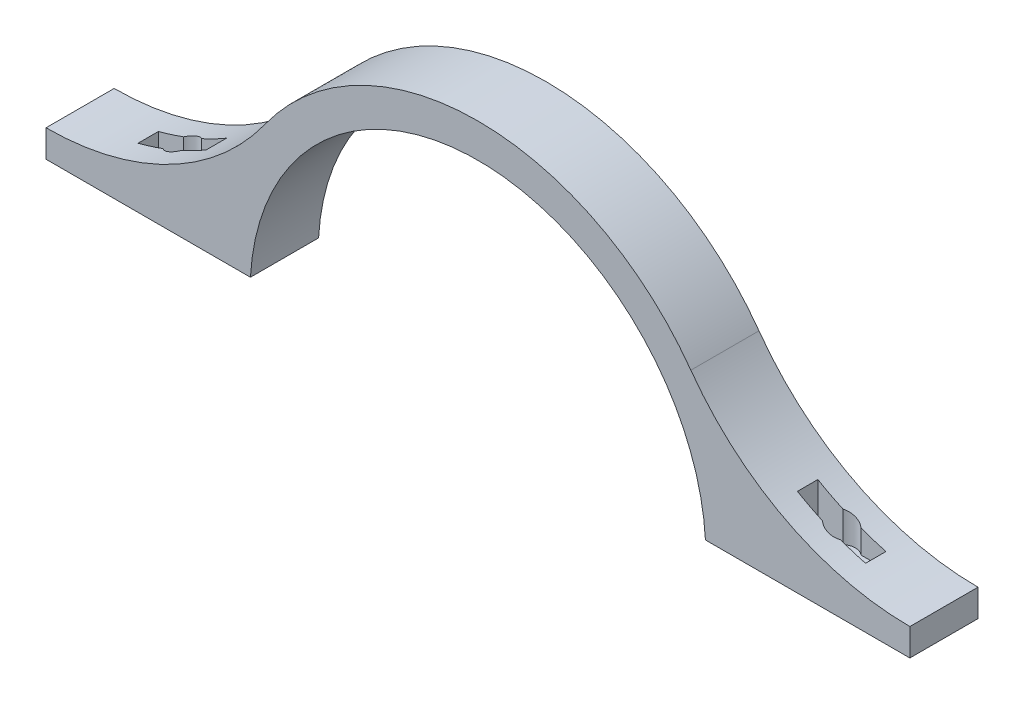
SolidWorks part; units mm, degrees
material "PET"
ref_plane "Front Plane" through (0, 0, 0) normal (0, 0, 1) x (1, 0, 0)
ref_plane "Top Plane" through (0, 0, 0) normal (0, 1, 0) x (1, 0, 0)
ref_plane "Right Plane" through (0, 0, 0) normal (1, 0, 0) x (0, 0, -1)
sketch "Sketch1" plane through (0, 0, 0) normal (0, 0, 1) x (1, 0, 0)
  line L1 (-160.9976, 4.7625) -> (-160.9976, 14.9225)
  line L3 (0, 97.6312) -> (0, 84.9312)
  line L5 (0, 4.7625) -> (-84.7976, 4.7625) construction
  line L6 (0, 0) -> (0, 4.7625)
  line L8 (-84.7976, 4.7625) -> (-160.9976, 4.7625)
  arc A0 (0, 97.6312) -> (-79.3657, 56.859) centre (0, 0) ccw
  circle A5 centre (0, 0) radius 97.6313 construction
  circle A6 centre (0, 0) radius 84.9312 construction
  arc A7 (0, 84.9312) -> (-84.7976, 4.7625) centre (0, 0) ccw
  circle A8 centre (0, 0) radius 84.9312 construction
  arc A10 (-160.9976, 14.9225) -> (-79.3657, 56.859) centre (-160.9976, 115.3415) ccw
  dimension "D3" = 10.16
  dimension "D1" = 12.7
  dimension "D2" = 76.2
  dimension "D5" = 4.7625
extrude "Boss-Extrude1" add sketch "Sketch1" against normal blind 25.4 contours A10 L1 L8 A7 L3 A0
sketch "Sketch3" plane through (0, 4.7625, 0) normal (0, -1, 0) x (1, 0, 0)
  line L0 (-122.8976, 0) -> (-122.8976, -12.7) construction
  line L1 (-84.7976, 0) -> (-160.9976, 0) construction
  line L2 (-122.8976, -12.7) -> (-160.9976, -12.7) construction
  line L3 (-160.9976, -25.4) -> (-160.9976, 0) construction
  line L4 (-119.5375, -16.51) -> (-110.1976, -16.51)
  line L5 (-135.5976, -8.89) -> (-126.2577, -8.89)
  line L6 (-135.5976, -8.89) -> (-135.5976, -16.51)
  line L7 (-135.5976, -16.51) -> (-126.2577, -16.51)
  line L8 (-110.1976, -8.89) -> (-110.1976, -16.51)
  line L9 (-135.5976, -8.89) -> (-110.1976, -16.51) construction
  line L10 (-135.5976, -16.51) -> (-110.1976, -8.89) construction
  line L11 (-119.5375, -8.89) -> (-110.1976, -8.89)
  arc A0 (-126.2577, -16.51) -> (-119.5375, -16.51) centre (-122.8976, -12.7) ccw
  arc A1 (-119.5375, -8.89) -> (-126.2577, -8.89) centre (-122.8976, -12.7) ccw
  dimension "D1" = 10.16
  dimension "D2" = 25.4
  dimension "D3" = 7.62
extrude "Cut-Extrude2" cut sketch "Sketch3" against normal up to surface (23.9572 mm away)
mirror "Mirror2" about plane through (0, 0, -25.4) normal (-1, 0, 0) of "Boss-Extrude1", "Cut-Extrude2"
sketch "Sketch4" plane through (0, 4.7625, 0) normal (0, -1, 0) x (1, 0, 0)
  line L0 (-110.1976, -8.89) -> (-119.5375, -8.89) construction
  line L1 (-110.1976, -16.51) -> (-110.1976, -8.89) construction
  line L2 (-119.5375, -16.51) -> (-110.1976, -16.51) construction
  line L3 (-135.5976, -16.51) -> (-126.2577, -16.51) construction
  line L4 (-135.5976, -8.89) -> (-135.5976, -16.51) construction
  line L5 (-126.2577, -8.89) -> (-135.5976, -8.89) construction
  line L6 (-110.1976, -8.89) -> (-119.5375, -8.89)
  line L7 (-110.1976, -16.51) -> (-110.1976, -8.89)
  line L8 (-119.5375, -16.51) -> (-110.1976, -16.51)
  line L9 (-135.5976, -16.51) -> (-126.2577, -16.51)
  line L10 (-135.5976, -8.89) -> (-135.5976, -16.51)
  line L11 (-126.2577, -8.89) -> (-135.5976, -8.89)
  arc A0 (-119.5375, -8.89) -> (-126.2577, -8.89) centre (-122.8976, -12.7) ccw
  circle A6 centre (-122.8976, -12.7) radius 2.159
  circle A7 centre (-122.8976, -12.7) radius 5.08 construction
  arc A8 (-126.2577, -16.51) -> (-119.5375, -16.51) centre (-122.8976, -12.7) ccw
  dimension "D1" = 4.318
extrude "Boss-Extrude2" add sketch "Sketch4" against normal blind 7.62
mirror "Mirror3" about plane through (0, 0, 0) normal (1, 0, 0) of "Boss-Extrude2"
